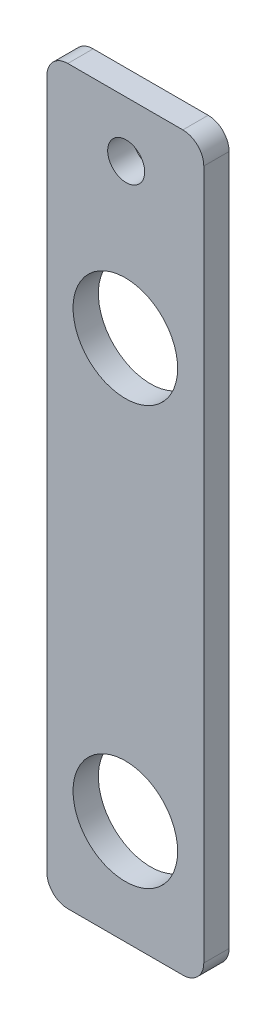
SolidWorks part; units mm, degrees
material "Acrylic (Medium-high impact)"
ref_plane "Front Plane" through (0, 0, 0) normal (0, 0, 1) x (1, 0, 0)
ref_plane "Top Plane" through (0, 0, 0) normal (0, 1, 0) x (1, 0, 0)
ref_plane "Right Plane" through (0, 0, 0) normal (1, 0, 0) x (0, 0, -1)
sketch "Sketch1" plane through (0, 0, 0) normal (0, 0, 1) x (1, 0, 0)
  line L0 (9.525, 0) -> (9.525, 88.9) construction
  line L1 (0, 0) -> (19.05, 0)
  line L2 (0, 0) -> (0, 88.9)
  line L3 (0, 88.9) -> (19.05, 88.9)
  line L4 (19.05, 0) -> (19.05, 88.9)
  circle A0 centre (9.525, 12.7) radius 6.35
  circle A1 centre (9.525, 63.5) radius 6.35
  dimension "D1" = 12.7
  dimension "D2" = 12.7
  dimension "D3" = 25.4
  dimension "D4" = 50.8
  dimension "D5" = 19.05
  dimension "D6" = 12.7
extrude "Boss-Extrude1" add sketch "Sketch1" along normal blind 3.0734
hole_wizard "#8 Clearance Hole1" positions "Sketch2" profile "Sketch3" hole size "#8" standard "ANSI Inch" end condition through all
sketch "Sketch2" plane through (0, 0, 3.0734) normal (0, 0, 1) x (1, 0, 0)
  line L0 (9.525, 88.9) -> (9.525, 0) construction
  line L1 (19.05, 88.9) -> (0, 88.9) construction
  line L2 (0, 0) -> (19.05, 0) construction
  point P0 (9.6275, 82.1563)
  dimension "D1" = 6.7437
sketch "Sketch3" plane through (9.6275, 82.1563, 3.0734) normal (1, 0, 0) x (0, -1, 0)
  line L0 (0, 0) -> (0, 3.0734)
  line L1 (0, 3.0734) -> (2.2479, 3.0734)
  line L2 (2.2479, 3.0734) -> (2.2479, 0)
  line L5 (2.2479, 0) -> (0, 0)
  line L11 (0, -6.35) -> (0, 107.95) construction
  dimension "Thru Hole Dia." = 4.4958
  dimension "Thru Hole Depth" = 3.0734
fillet "Fillet1" radius 2.54 4 edges at (0, 0, 1.5367) (19.05, 0, 1.5367) (19.05, 88.9, 1.5367) (0, 88.9, 1.5367)
